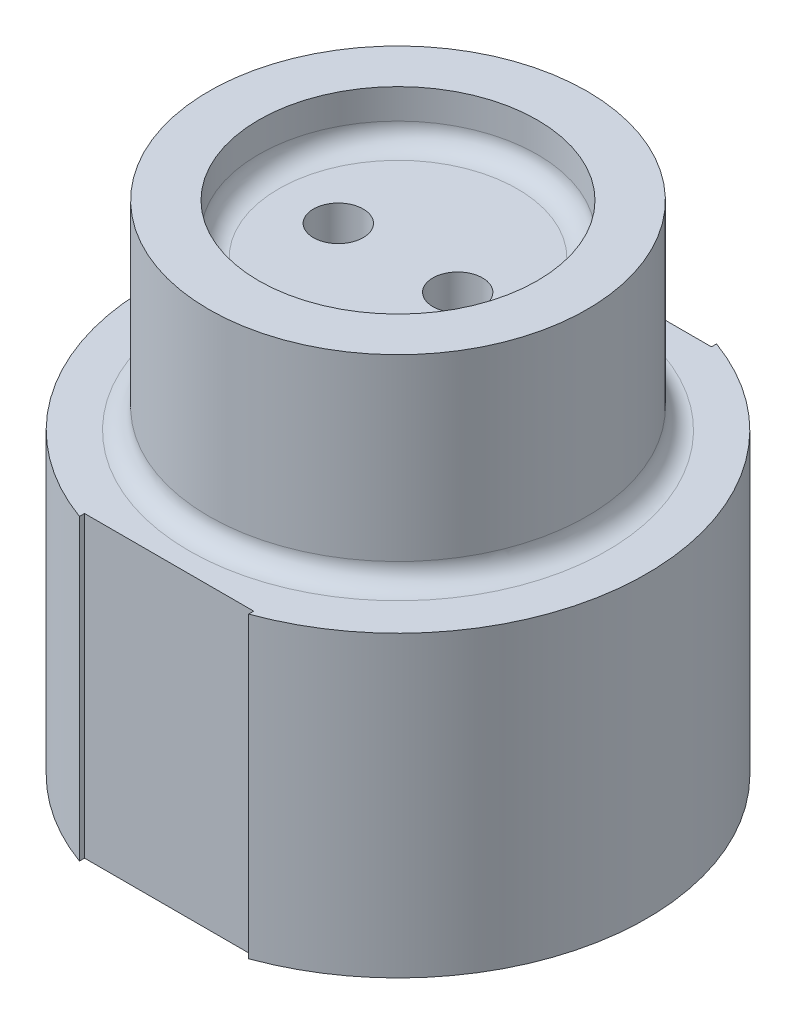
SolidWorks part; units mm, degrees
ref_plane "Front Plane" through (0, 0, 0) normal (0, 0, 1) x (1, 0, 0)
ref_plane "Top Plane" through (0, 0, 0) normal (0, 1, 0) x (1, 0, 0)
ref_plane "Right Plane" through (0, 0, 0) normal (1, 0, 0) x (0, 0, -1)
sketch "Sketch3" plane through (0, 0, 0) normal (0, 0, 1) x (1, 0, 0)
  line L0 (0, 0) -> (63.5, 0)
  line L1 (63.5, 0) -> (63.5, 76.2)
  line L2 (63.5, 76.2) -> (48.26, 76.2)
  line L3 (48.26, 76.2) -> (48.26, 127)
  line L4 (0, 12.7) -> (50.8, 12.7)
  line L5 (50.8, 12.7) -> (50.8, 63.5)
  line L6 (50.8, 63.5) -> (35.56, 63.5)
  line L7 (35.56, 63.5) -> (35.56, 127)
  line L8 (48.26, 127) -> (35.56, 127)
  line L9 (0, 12.7) -> (0, 0)
  dimension "D1" = 63.5
  dimension "D2" = 76.2
  dimension "D3" = 50.8
  dimension "D4" = 15.24
  dimension "D5" = 12.7
revolve "Revolve1" add sketch "Sketch3" angle 360 about L9
ref_plane "Plane1" through (0, 114.3, 0) normal (0, 1, 0) x (1, 0, 0)
sketch "Sketch4" plane through (0, 114.3, 0) normal (0, 1, 0) x (1, 0, 0)
  circle A0 centre (0, 0) radius 35.56
  circle A1 centre (0, 0) radius 35.56 construction
extrude "Boss-Extrude1" add sketch "Sketch4" against normal blind 7.62
sketch "Sketch5" plane through (0, 114.3, 0) normal (0, 1, 0) x (1, 0, 0)
  circle A0 centre (15.24, 0) radius 6.35
  circle A1 centre (15.24, 0) radius 8.89
  point P2 (0, 0)
  dimension "D1" = 12.7
  dimension "D2" = 15.24
  dimension "D3" = 2.54
sketch "Sketch6" plane through (0, 0, 0) normal (0, 0, 1) x (1, 0, 0)
  line L0 (15.24, 114.3) -> (15.24, 50.8)
  line L1 (21.59, 114.3) -> (8.89, 114.3) construction
  line L2 (15.24, 50.8) -> (33.02, 50.8)
  line L3 (33.02, 50.8) -> (33.02, 12.7)
  line L4 (50.8, 12.7) -> (-50.8, 12.7) construction
  line L5 (-63.5, 0) -> (63.5, 0) construction
  point P4 (0, 0)
  dimension "D1" = 50.8
  dimension "D2" = 17.78
sweep "Sweep1" add profiles "Sketch5" path "Sketch6"
sketch "Sketch7" plane through (0, 12.7, 0) normal (0, 1, 0) x (1, 0, 0)
  circle A0 centre (33.02, 0) radius 6.35
  circle A1 centre (33.02, 0) radius 6.35 construction
extrude "Cut-Extrude1" cut sketch "Sketch7" against normal through all
sketch "Sketch8" plane through (0, 106.68, 0) normal (0, -1, 0) x (1, 0, 0)
  circle A0 centre (15.24, 0) radius 6.35
  circle A1 centre (15.24, 0) radius 6.35 construction
extrude "Cut-Extrude2" cut sketch "Sketch8" against normal up to next (7.62 mm away)
mirror "Mirror1" about plane through (0, 0, 0) normal (1, 0, 0) of "Cut-Extrude2", "Sweep1", "Cut-Extrude1"
ref_plane "Plane2" through (0, 0, 63.5) normal (0, 0, 1) x (1, 0, 0)
sketch "Sketch10" plane through (0, 0, 63.5) normal (0, 0, 1) x (1, 0, 0)
  line L0 (-63.5, 0) -> (63.5, 0) construction
  line L1 (-21.59, 0) -> (21.59, 0)
  line L2 (-21.59, 0) -> (-21.59, 76.2)
  line L3 (-21.59, 76.2) -> (21.59, 76.2)
  line L4 (21.59, 0) -> (21.59, 76.2)
  line L5 (63.5, 76.2) -> (-63.5, 76.2) construction
  point P8 (0, 0)
  dimension "D1" = 43.18
extrude "Cut-Extrude3" cut sketch "Sketch10" against normal blind 5.08
mirror "Mirror2" about plane through (0, 0, 0) normal (0, 0, 1) of "Cut-Extrude3"
fillet "Fillet1" radius 5.08 1 edges at (0, 114.3, 35.56)
fillet "Fillet2" radius 5.08 1 edges at (0, 76.2, 48.26)
